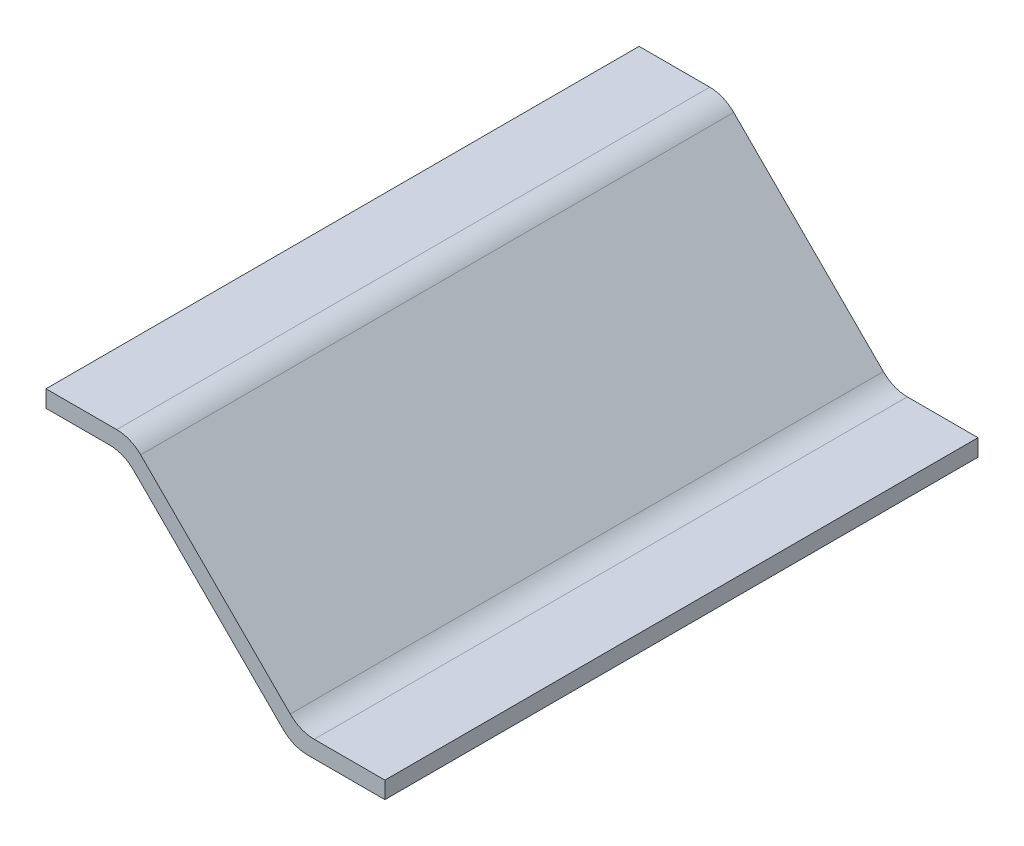
SolidWorks part; units mm, degrees
ref_plane "Front Plane" through (0, 0, 0) normal (0, 0, 1) x (1, 0, 0)
ref_plane "Top Plane" through (0, 0, 0) normal (0, 1, 0) x (1, 0, 0)
ref_plane "Right Plane" through (0, 0, 0) normal (1, 0, 0) x (0, 0, -1)
sketch "Sketch4" plane through (0, 0, 0) normal (0, 0, 1) x (1, 0, 0)
  line L0 (0, 0) -> (0.5, 0)
  line L1 (0.5, 0) -> (1.5, -1)
  line L2 (1.5, -1) -> (2, -1)
  line L3 (0, -0.1) -> (0.4586, -0.1)
  line L4 (0.4586, -0.1) -> (1.4586, -1.1)
  line L5 (1.4586, -1.1) -> (2, -1.1)
  line L6 (0, -0.1) -> (0, 0)
  line L7 (2, -1.1) -> (2, -1)
  dimension "D1" = 1
  dimension "D2" = 0.5
  dimension "D3" = 0.5
  dimension "D4" = 1
  dimension "D5" = 0.1
extrude "Boss-Extrude1" add sketch "Sketch4" along normal mid plane 3.5
fillet "Fillet4" radius 0.2 4 edges at (0.4586, -0.1, 0) (1.4586, -1.1, 0) (1.5, -1, 0) (0.5, 0, 0)
